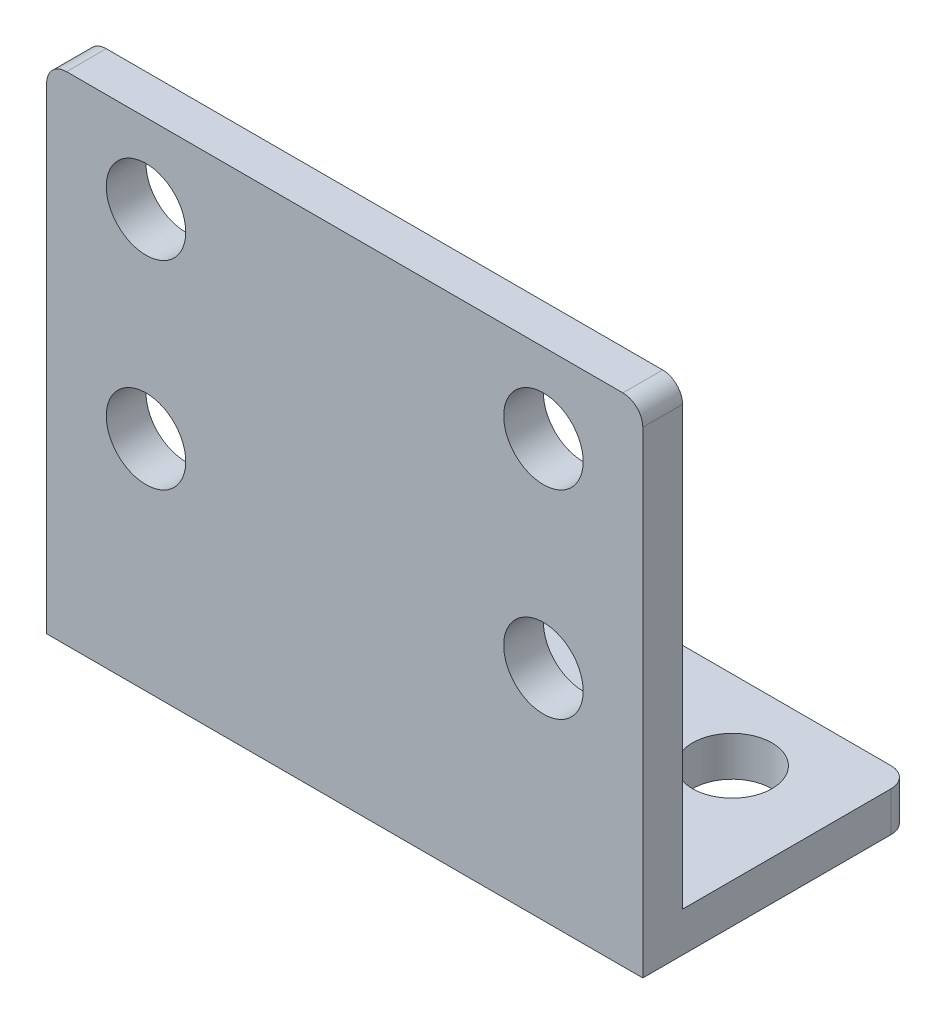
SolidWorks part; units mm, degrees
ref_plane "Front Plane" through (0, 0, 0) normal (0, 0, 1) x (1, 0, 0)
ref_plane "Top Plane" through (0, 0, 0) normal (0, 1, 0) x (1, 0, 0)
ref_plane "Right Plane" through (0, 0, 0) normal (1, 0, 0) x (0, 0, -1)
sketch "Sketch1" plane through (0, 0, 0) normal (1, 0, 0) x (0, 0, -1)
  line L0 (0, 0) -> (0, 50)
  line L1 (0, 50) -> (4, 50)
  line L2 (4, 50) -> (4, 4)
  line L3 (4, 4) -> (27, 4)
  line L4 (27, 4) -> (27, 0)
  line L5 (27, 0) -> (0, 0)
  dimension "D1" = 4
  dimension "D2" = 4
  dimension "D3" = 50
  dimension "D4" = 27
extrude "Boss-Extrude1" add sketch "Sketch1" along normal blind 60
sketch "Sketch8" plane through (0, 0, 0) normal (0, 0, 1) x (1, 0, 0)
  circle A0 centre (10, 22) radius 4 construction
  circle A1 centre (50, 22) radius 4 construction
  circle A2 centre (50, 42) radius 4 construction
  circle A3 centre (10, 42) radius 4 construction
  circle A4 centre (10, 22) radius 4
  circle A5 centre (50, 22) radius 4
  circle A6 centre (50, 42) radius 4
  circle A7 centre (10, 42) radius 4
extrude "Cut-Extrude3" cut sketch "Sketch8" against normal up to next
sketch "Sketch9" plane through (0, 0, 0) normal (0, -1, 0) x (1, 0, 0)
  circle A0 centre (50, -19) radius 4 construction
  circle A1 centre (10, -19) radius 4 construction
  circle A2 centre (50, -19) radius 4
  circle A3 centre (10, -19) radius 4
extrude "Cut-Extrude4" cut sketch "Sketch9" against normal up to next
fillet "Fillet2" radius 2 4 edges at (60, 2, -27) (0, 2, -27) (60, 50, -2) (0, 50, -2)
